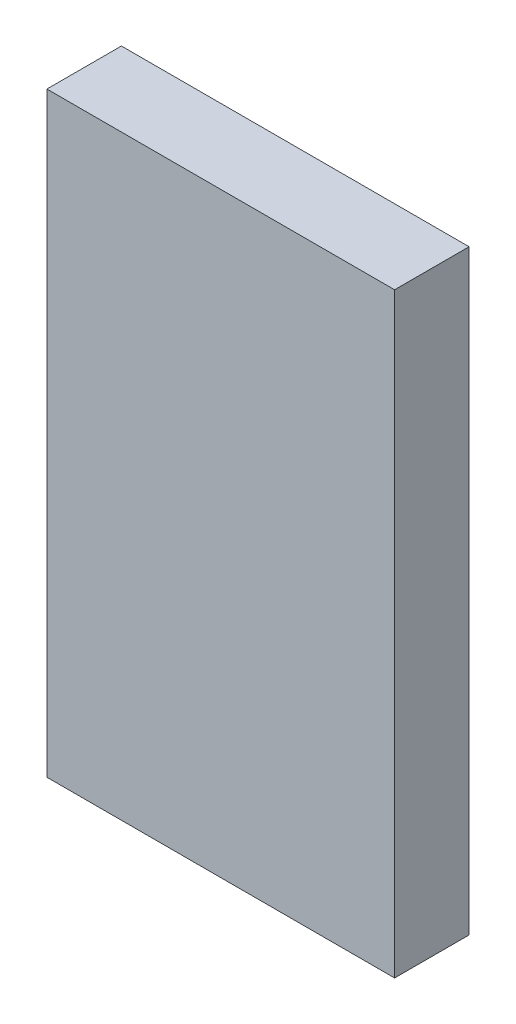
SolidWorks part; units mm, degrees
ref_plane "Front Plane" through (0, 0, 0) normal (0, 0, 1) x (1, 0, 0)
ref_plane "Top Plane" through (0, 0, 0) normal (0, 1, 0) x (1, 0, 0)
ref_plane "Right Plane" through (0, 0, 0) normal (1, 0, 0) x (0, 0, -1)
sketch "Sketch1" plane through (0, 0, 0) normal (0, 0, 1) x (1, 0, 0)
  line L1 (0, 0) -> (35.56, 0)
  line L2 (0, 0) -> (0, 60.96)
  line L3 (0, 60.96) -> (35.56, 60.96)
  line L4 (35.56, 0) -> (35.56, 60.96)
  dimension "D1" = 60.96
  dimension "D2" = 35.56
extrude "Boss-Extrude1" add sketch "Sketch1" along normal blind 7.62
